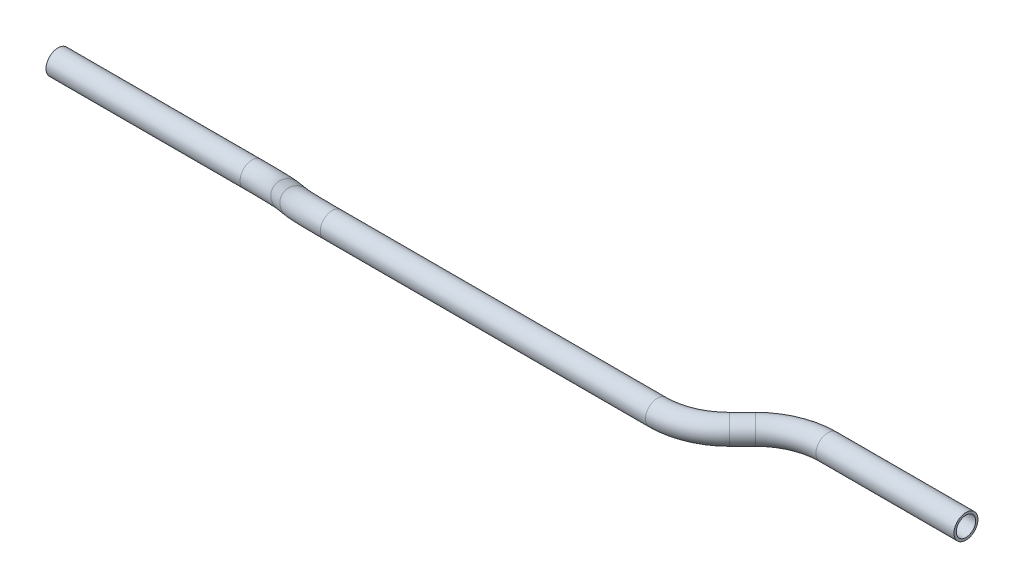
SolidWorks part; units mm, degrees
material "AISI Type 316L stainless steel"
ref_plane "Front Plane" through (0, 0, 0) normal (0, 0, 1) x (1, 0, 0)
ref_plane "Top Plane" through (0, 0, 0) normal (0, 1, 0) x (1, 0, 0)
ref_plane "Right Plane" through (0, 0, 0) normal (1, 0, 0) x (0, 0, -1)
sketch3d "3DSketch2"
  line L0 (0, 0, 0) -> (102.4571, 0, 0)
  line L1 (0, 27.2535, 0) -> (0, 27.2535, 29.21) construction
  line L2 (0, 27.2535, 29.21) -> (467.4369, 27.2535, 29.21) construction
  line L3 (129.3979, 7.6128, 8.1593) -> (147.0291, 19.6407, 21.0507)
  line L4 (406.3799, 27.2535, 0) -> (479.2518, 27.2535, 0)
  line L5 (0, 0, 0) -> (0, 27.2535, 0) construction
  line L6 (0, 27.2535, 0) -> (467.4369, 27.2535, 0) construction
  line L7 (173.9699, 27.2535, 29.21) -> (345.6068, 27.2535, 29.21)
  line L8 (372.5476, 27.2535, 18.0508) -> (379.4391, 27.2535, 11.1592)
  arc A0 (379.4391, 27.2535, 11.1592) -> (406.3799, 27.2535, 0) centre (406.3799, 27.2535, 38.1) ccw
  arc A1 (345.6068, 27.2535, 29.21) -> (372.5476, 27.2535, 18.0508) centre (345.6068, 27.2535, -8.89) ccw
  arc A2 (147.0291, 19.6407, 21.0507) -> (173.9699, 27.2535, 29.21) centre (173.9699, 1.2619, 1.3524) ccw
  arc A3 (102.4571, 0, 0) -> (129.3979, 7.6128, 8.1593) centre (102.4571, 25.9917, 27.8576) ccw
  point P7 (390.5984, 27.2535, 0)
  point P9 (406.3799, -10.8465, 38.1)
  point P12 (361.3884, 27.2535, 29.21)
  point P14 (345.6068, 65.3535, -8.89)
  point P17 (158.1884, 27.2535, 29.21)
  point P19 (173.9699, 29.1194, -24.6392)
  point P22 (118.2387, 0, 0)
  point P26 (102.4571, -1.8659, 53.8492)
  dimension "D5" = 203.2
  dimension "D10" = 27.2535
  dimension "D7" = 38.1
  dimension "D1" = 118.2387
  dimension "D2" = 29.21
  dimension "D3" = 45
  dimension "D4" = 135
  dimension "D6" = 88.6535
  dimension "D11" = 467.4369
ref_plane "Plane1" through (0, 0, 0) normal (1, 0, 0) x (0, 0, -1)
sketch "Sketch1" plane through (0, 0, 0) normal (1, 0, 0) x (0, 0, -1)
  circle A0 centre (0, 0) radius 6.35
  circle A1 centre (0, 0) radius 5.1054
  dimension "D1" = 12.7
  dimension "D2" = 1.2446
sweep "Sweep2" add profiles "Sketch1" path "3DSketch2"
